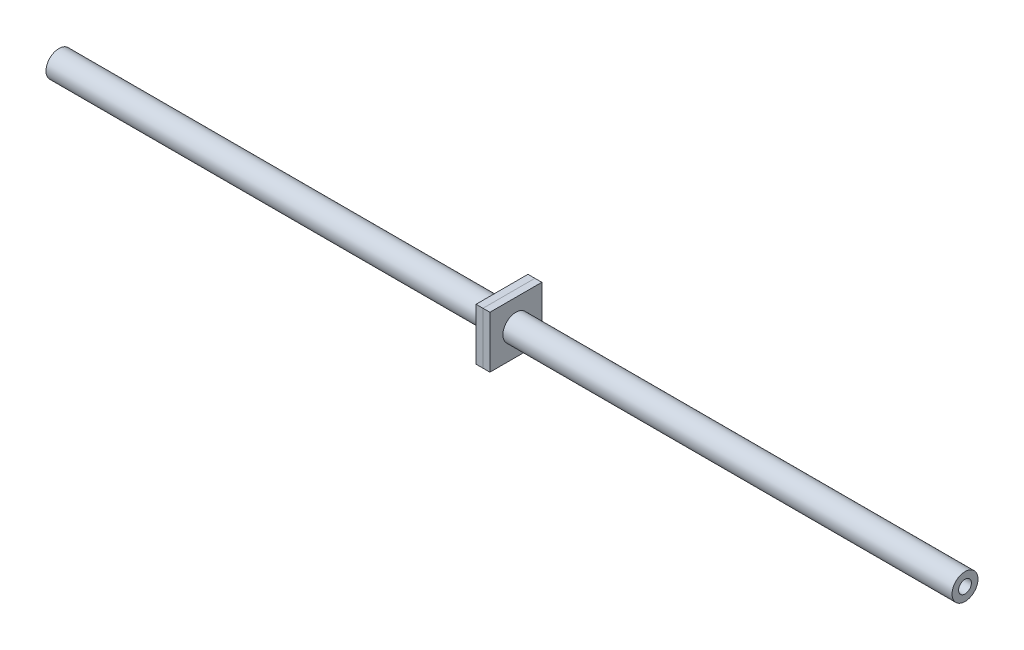
SolidWorks part; units mm, degrees
material "AISI 4130 Steel, normalized at 870C"
ref_plane "Front Plane" through (0, 0, 0) normal (0, 0, 1) x (1, 0, 0)
ref_plane "Top Plane" through (0, 0, 0) normal (0, 1, 0) x (1, 0, 0)
ref_plane "Right Plane" through (0, 0, 0) normal (1, 0, 0) x (0, 0, -1)
sketch "Toe Rod" plane through (0, 0, 0) normal (0, 0, 1) x (1, 0, 0)
  line L0 (0, 0) -> (332.4405, 0)
  line L1 (0, 0) -> (-26.9748, 0) construction
  line L2 (332.4405, 0) -> (359.4153, 0) construction
  dimension "D1" = 26.9748
  dimension "D2" = 386.3901
other "Toe Rod Member"
ref_plane "Plane1" through (0, 0, 0) normal (1, 0, 0) x (0, 1, 0)
sketch "Sketch1" plane through (0, 0, 0) normal (1, 0, 0) x (0, 1, 0)
  circle A0 centre (0, 0) radius 4.7625
  circle A1 centre (0, 0) radius 2.3495
  point P3 (0, 0)
  dimension "D1" = 9.525
  dimension "D2" = 2.413
sketch "Sketch2" plane through (0, 0, 0) normal (1, 0, 0) x (0, 0, -1)
  line L1 (9.525, 9.525) -> (-9.525, 9.525)
  line L2 (9.525, 9.525) -> (9.525, -9.525)
  line L3 (9.525, -9.525) -> (-9.525, -9.525)
  line L4 (-9.525, 9.525) -> (-9.525, -9.525)
  line L5 (9.525, 9.525) -> (-9.525, -9.525) construction
  line L6 (9.525, -9.525) -> (-9.525, 9.525) construction
  circle A0 centre (0, 0) radius 4.7625 construction
  circle A1 centre (0, 0) radius 4.7625
  point P0 (0, 0)
  dimension "D1" = 19.05
extrude "Toe Rod Nut 1" add sketch "Sketch2" along normal blind 2.54 from offset 165.1 separate body
sketch "Sketch3" plane through (0, 0, 0) normal (1, 0, 0) x (0, 0, -1)
  line L0 (9.525, 9.525) -> (-9.525, 9.525) construction
  line L1 (9.525, 9.525) -> (9.525, -9.525) construction
  line L2 (-9.525, 9.525) -> (-9.525, -9.525) construction
  line L3 (9.525, -9.525) -> (-9.525, -9.525) construction
  line L4 (9.525, 9.525) -> (-9.525, 9.525)
  line L5 (9.525, 9.525) -> (9.525, -9.525)
  line L6 (-9.525, 9.525) -> (-9.525, -9.525)
  line L7 (9.525, -9.525) -> (-9.525, -9.525)
  circle A0 centre (0, 0) radius 4.7625 construction
  circle A1 centre (0, 0) radius 4.7625
extrude "Toe Rod Nut 2" add sketch "Sketch3" against normal blind 2.54 from surface at 165.1 separate body starting at face at (165.1, 0, 0)
